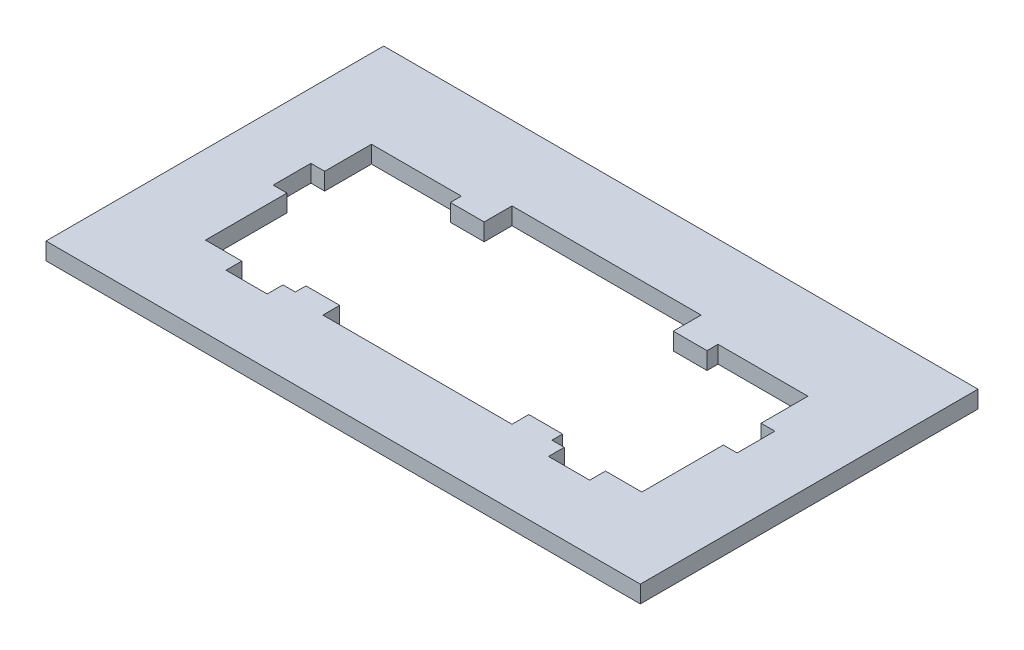
SolidWorks part; units mm, degrees
ref_plane "Front" through (0, 0, 0) normal (0, 0, 1) x (1, 0, 0)
ref_plane "Top" through (0, 0, 0) normal (0, 1, 0) x (1, 0, 0)
ref_plane "Right" through (0, 0, 0) normal (1, 0, 0) x (0, 0, -1)
sketch "Sketch1" plane through (0, 0, 0) normal (0, 1, 0) x (1, 0, 0)
  line L0 (-7, 4.9392) -> (-9.4996, 4.9392)
  line L1 (-22, 12.5) -> (22, 12.5)
  line L2 (-22, 12.5) -> (-22, -12.5)
  line L3 (-22, -12.5) -> (22, -12.5)
  line L4 (22, 12.5) -> (22, -12.5)
  line L5 (-22, 12.5) -> (22, -12.5) construction
  line L6 (-22, -12.5) -> (22, 12.5) construction
  line L7 (-7, 7) -> (7, 7)
  line L8 (-7, 7) -> (-7, -7)
  line L9 (-7, -7) -> (7, -7)
  line L10 (7, 7) -> (7, -7)
  line L11 (-7, 7) -> (7, -7) construction
  line L12 (-7, -7) -> (7, 7) construction
  line L13 (-9.4996, 4.9392) -> (-9.4996, 5.752)
  line L14 (-9.4996, 5.752) -> (-16.1544, 5.752)
  line L15 (-16.1544, 5.752) -> (-16.1544, 2.286)
  line L16 (-16.1544, 2.286) -> (-17.1742, 2.286)
  line L17 (-17.1742, 2.286) -> (-17.1742, -0.508)
  line L18 (-17.1742, -0.508) -> (-16.1544, -0.508)
  line L19 (-16.1544, -0.508) -> (-16.1544, -6.5416)
  line L20 (-16.1544, -6.5416) -> (-13.462, -6.5416)
  line L21 (-13.462, -6.5416) -> (-13.462, -7.71)
  line L22 (-13.462, -7.71) -> (-10.414, -7.71)
  line L23 (-10.414, -7.71) -> (-10.414, -6.5416)
  line L24 (-10.414, -6.5416) -> (-9.4996, -6.5416)
  line L25 (-9.4996, -6.5416) -> (-9.4996, -5.7542)
  line L26 (-9.4996, -5.7542) -> (-7, -5.7542)
  line L27 (0, 0) -> (-28.61, 0) construction
  line L28 (-11.938, -7.71) -> (-11.938, 13.6054) construction
  line L29 (0, 0) -> (0, 7) construction
  line L30 (9.4996, -5.7542) -> (7, -5.7542)
  line L31 (7, 4.9392) -> (9.4996, 4.9392)
  line L32 (9.4996, -6.5416) -> (9.4996, -5.7542)
  line L33 (10.414, -6.5416) -> (9.4996, -6.5416)
  line L34 (10.414, -7.71) -> (10.414, -6.5416)
  line L35 (13.462, -7.71) -> (10.414, -7.71)
  line L36 (13.462, -6.5416) -> (13.462, -7.71)
  line L37 (16.1544, -6.5416) -> (13.462, -6.5416)
  line L38 (16.1544, -0.508) -> (16.1544, -6.5416)
  line L39 (17.1742, -0.508) -> (16.1544, -0.508)
  line L40 (17.1742, 2.286) -> (17.1742, -0.508)
  line L41 (16.1544, 2.286) -> (17.1742, 2.286)
  line L42 (16.1544, 5.752) -> (16.1544, 2.286)
  line L43 (9.4996, 5.752) -> (16.1544, 5.752)
  line L44 (9.4996, 4.9392) -> (9.4996, 5.752)
  line L45 (11.938, -7.71) -> (11.938, 13.6054) construction
  point P0 (0, 0)
  point P6 (0, 0)
  dimension "D1" = 44
  dimension "D2" = 25
  dimension "D3" = 14
  dimension "D4" = 14
  dimension "D5" = 6.6548
  dimension "D6" = 0.8128
  dimension "D7" = 2.794
  dimension "D8" = 0.508
  dimension "D9" = 6.5416
  dimension "D10" = 3.048
  dimension "D11" = 12.2936
  dimension "D12" = 0.7874
  dimension "D13" = 13.462
  dimension "D14" = 23.876
  dimension "D15" = 4.2164
extrude "Boss-Extrude1" add sketch "Sketch1" along normal blind 1.524 contours L4 L1 L2 L3 L31 L44 L43 L42 L41 L40 L39 L38 L37 L36 L35 L34 L33 L32 L30 L10 L9 L8 L26 L25 L24 L23 L22 L21 L20 L19 L18 L17 L16 L15 L14 L13 L0 L7
chamfer "Chamfer1" distance 0.25 angle 45 40 edges at (9.4996, 0, -5.3456) (12.827, 0, -5.752) (16.1544, 0, -4.019) (16.6643, 0, -2.286) (17.1742, 0, -0.889) (16.6643, 0, 0.508) (16.1544, 0, 3.5248) (14.8082, 0, 6.5416) (13.462, 0, 7.1258) (11.938, 0, 7.71) (10.414, 0, 7.1258) (9.9568, 0, 6.5416) (9.4996, 0, 6.1479) (8.2498, 0, 5.7542) (7, 0, 6.3771) (0, 0, 7) (-7, 0, 6.3771) (-8.2498, 0, 5.7542) (-9.4996, 0, 6.1479) (-9.9568, 0, 6.5416) (-10.414, 0, 7.1258) (-11.938, 0, 7.71) (-13.462, 0, 7.1258) (-14.8082, 0, 6.5416) (-16.1544, 0, 3.5248) (-16.6643, 0, 0.508) (-17.1742, 0, -0.889) (-16.6643, 0, -2.286) (-16.1544, 0, -4.019) (-12.827, 0, -5.752) (-9.4996, 0, -5.3456) (-8.2498, 0, -4.9392) (-7, 0, -5.9696) (0, 0, -7) (7, 0, -5.9696) (8.2498, 0, -4.9392) (0, 0, -12.5) (-22, 0, 0) (0, 0, 12.5) (22, 0, 0)
